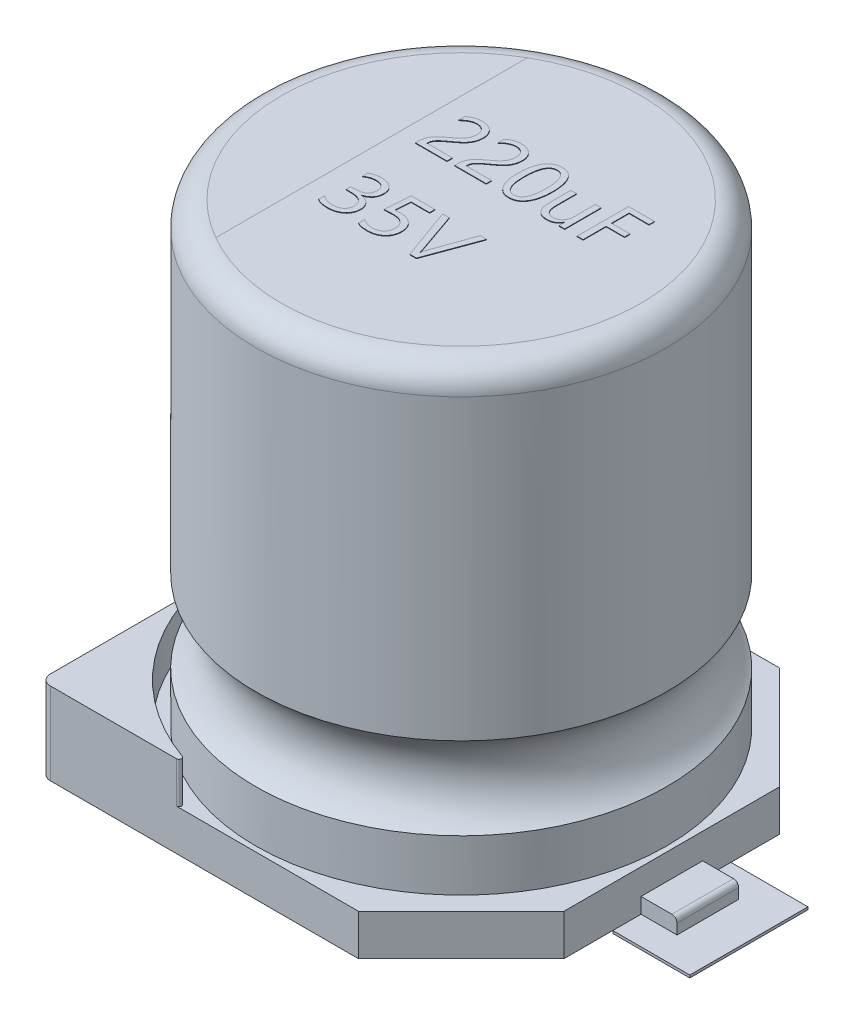
SolidWorks part; units mm, degrees
ref_plane "Front Plane" through (0, 0, 0) normal (0, 0, 1) x (1, 0, 0)
ref_plane "Top Plane" through (0, 0, 0) normal (0, 1, 0) x (1, 0, 0)
ref_plane "Right Plane" through (0, 0, 0) normal (1, 0, 0) x (0, 0, -1)
sketch "Sketch1" plane through (0, 0, 0) normal (0, 1, 0) x (1, 0, 0)
  circle A0 centre (0, 0) radius 4
  dimension "D1" = 8
extrude "Boss-Extrude1" add sketch "Sketch1" along normal blind 8.9
sketch "Sketch2" plane through (0, 0, 0) normal (0, 0, 1) x (1, 0, 0)
  line L0 (-4, 8.9) -> (-4, 0) construction
  line L1 (-4, 2.6) -> (-4, 1)
  line L2 (0, 0) -> (0, 2.8507) construction
  arc A0 (-4, 2.6) -> (-4, 1) centre (-4.6, 1.8) cw
  dimension "D1" = 1
  dimension "D2" = 1
  dimension "D3" = 0.6
revolve "Cut-Revolve1" cut sketch "Sketch2" angle 360 about L2
fillet "Fillet1" radius 0.5 1 edges at (0, 8.9, 4)
sketch "Sketch3" plane through (0, 0, 0) normal (0, -1, 0) x (1, 0, 0)
  line L1 (4.1, -4.1) -> (-4.1, -4.1)
  line L2 (4.1, -4.1) -> (4.1, 4.1)
  line L3 (4.1, 4.1) -> (-4.1, 4.1)
  line L4 (-4.1, -4.1) -> (-4.1, 4.1)
  line L5 (4.1, -4.1) -> (-4.1, 4.1) construction
  line L6 (4.1, 4.1) -> (-4.1, -4.1) construction
  circle A0 centre (0, 0) radius 4 construction
  point P0 (0, 0)
  dimension "D1" = 4.1
  dimension "D2" = 4.1
extrude "Boss-Extrude2" add sketch "Sketch3" along normal blind 0.8 separate body
chamfer "Chamfer1" distance 2 angle 45 2 edges at (4.1, -0.4, -4.1) (4.1, -0.4, 4.1)
sketch "Sketch4" plane through (0, 0, 0) normal (0, 1, 0) x (1, 0, 0)
  line L0 (2.1, -4.1) -> (-4.1, -4.1) construction
  line L1 (-4.1, -4.1) -> (-4.1, 4.1) construction
  line L2 (-4.1, 4.1) -> (2.1, 4.1) construction
  line L3 (-1.1192, -4.1) -> (-4.1, -4.1)
  line L4 (-4.1, -4.1) -> (-4.1, -1.1192)
  line L5 (-4.1, 4.1) -> (-1.1192, 4.1)
  line L6 (-4.1, 1.1192) -> (-4.1, 4.1)
  arc A0 (-4.1, -1.1192) -> (-1.1192, -4.1) centre (0, 0) ccw
  arc A1 (-1.1192, 4.1) -> (-4.1, 1.1192) centre (0, 0) ccw
  dimension "D1" = 8.5
extrude "Boss-Extrude3" add sketch "Sketch4" along normal blind 0.8
fillet "Fillet2" radius 0.05 4 edges at (-1.1192, 0.4, -4.1) (-4.1, 0.4, -1.1192) (-4.1, 0.4, 1.1192) (-1.1192, 0.4, 4.1)
sketch "Sketch5" plane through (-4.1, 0, 0) normal (-1, 0, 0) x (0, 0, 1)
  line L0 (4.1, -0.8) -> (-4.1, -0.8) construction
  line L1 (-0.6, -0.8) -> (0.6, -0.8)
  line L2 (-0.6, -0.8) -> (-0.6, -0.5)
  line L3 (-0.6, -0.5) -> (0.6, -0.5)
  line L4 (0.6, -0.8) -> (0.6, -0.5)
  point P6 (0, -0.5)
  dimension "D1" = 1.2
  dimension "D2" = 0.3
extrude "Boss-Extrude4" add sketch "Sketch5" along normal blind 0.7 separate body
fillet "Fillet3" radius 0.1 1 edges at (-4.8, -0.5, 0)
mirror "Mirror3" about plane through (0, 0, 0) normal (1, 0, 0) of bodies 106
fillet "Fillet4" radius 0.2 2 edges at (-4.1, 0, -4.1) (-4.1, 0, 4.1)
sketch "Sketch6" plane through (0, 8.9, 0) normal (0, 1, 0) x (1, 0, 0)
  line L0 (-1.7448, 3.0341) -> (-1.7448, -3.0341)
  circle A0 centre (0, 0) radius 3.5 construction
split line "Split Line1"
sketch "Sketch7" plane through (0, 8.9, 0) normal (0, 1, 0) x (1, 0, 0)
  text T0 "220uF" font "Yu Gothic UI" height 1
  text T1 "35V" font "Yu Gothic UI" height 1
extrude "Boss-Extrude5" add sketch "Sketch7" along normal blind 0.01
sketch "Sketch8" plane through (0, -0.8, 0) normal (0, -1, 0) x (1, 0, 0)
  line L0 (-4.1, 3.9) -> (-4.1, -3.9) construction
  line L1 (-4.1, 1.15) -> (-5.6, 1.15)
  line L2 (-4.1, 1.15) -> (-4.1, -1.15)
  line L3 (-4.1, -1.15) -> (-5.6, -1.15)
  line L4 (-5.6, 1.15) -> (-5.6, -1.15)
  line L5 (0, 0) -> (0, 1.5788) construction
  line L6 (5.6, 1.15) -> (5.6, -1.15)
  line L7 (4.1, -1.15) -> (5.6, -1.15)
  line L8 (4.1, 1.15) -> (4.1, -1.15)
  line L9 (4.1, 1.15) -> (5.6, 1.15)
  point P6 (-5.6, 0)
  dimension "D1" = 2.3
  dimension "D2" = 1.5
extrude "Boss-Extrude6" add sketch "Sketch8" along normal blind 0.05 separate body
